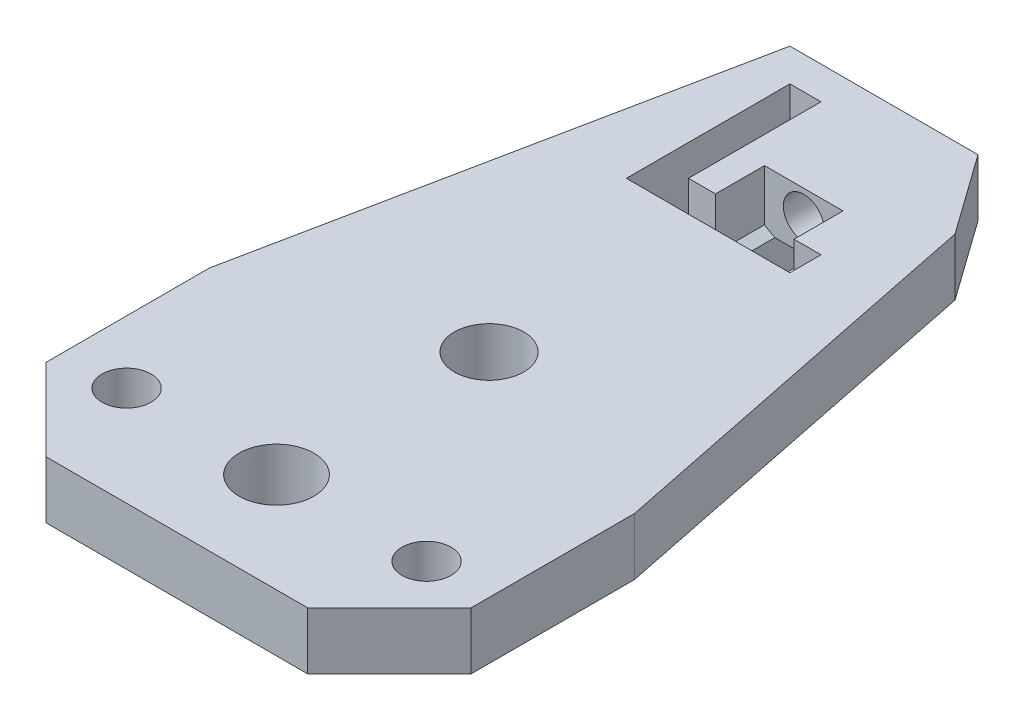
SolidWorks part; units mm, degrees
ref_plane "Front Plane" through (0, 0, 0) normal (0, 0, 1) x (1, 0, 0)
ref_plane "Top Plane" through (0, 0, 0) normal (0, 1, 0) x (1, 0, 0)
ref_plane "Right Plane" through (0, 0, 0) normal (1, 0, 0) x (0, 0, -1)
sketch "Sketch1" plane through (0, 0, 0) normal (0, 1, 0) x (1, 0, 0)
  line L0 (4, 24.01) -> (4, 4)
  line L1 (0, 0) -> (28.01, 0)
  line L2 (0, 0) -> (0, 28.01)
  line L3 (0, 28.01) -> (28.01, 28.01)
  line L4 (28.01, 0) -> (28.01, 28.01)
  line L5 (4, 4) -> (24.01, 4)
  line L6 (24.01, 4) -> (24.01, 7.8)
  line L7 (24.01, 7.8) -> (7.8, 7.8)
  line L8 (7.8, 7.8) -> (7.8, 24.01)
  line L9 (7.8, 24.01) -> (4, 24.01)
  line L10 (24.01, 4) -> (28.01, 4) construction
  line L11 (4, 4) -> (0, 4) construction
  line L12 (4, 4) -> (4, 0) construction
  line L13 (4, 24.01) -> (4, 28.01) construction
  line L14 (28.01, -31) -> (28.01, -61)
  line L15 (0, 0) -> (28.01, 0)
  line L16 (0, 0) -> (0, -61)
  line L17 (0, -61) -> (28.01, -61)
  line L18 (28.01, 0) -> (28.01, -61)
  line L19 (28.01, -61) -> (40.01, -61)
  line L20 (28.01, -61) -> (28.01, -31)
  line L22 (40.01, -61) -> (40.01, -31)
  line L29 (14.005, -61) -> (14.005, 28.01) construction
  line L30 (0, -31) -> (0, -61)
  line L31 (0, -61) -> (-12, -61)
  line L32 (-12, -61) -> (-12, -31)
  line L33 (0, -31) -> (-12, -31)
  line L35 (28.01, -31) -> (28.01, 28.01)
  line L36 (28.01, -61) -> (40.01, -61)
  line L37 (28.01, -61) -> (28.01, -31)
  line L38 (28.01, -31) -> (40.01, -31)
  line L39 (40.01, -61) -> (40.01, -31)
  line L40 (-12, -61) -> (0, -61)
  line L41 (-12, -61) -> (-12, -31)
  line L42 (-12, -31) -> (0, -31)
  line L43 (0, -61) -> (0, -31)
  line L44 (28.01, -31) -> (40.01, -31)
  line L45 (28.01, -31) -> (40.01, -31)
  line L46 (28.01, -31) -> (28.01, 28.01)
  line L49 (-12, -31) -> (0, -31)
  line L52 (0, -31) -> (0, 28.01)
  circle A0 centre (14, -22.8) radius 4.25
  circle A1 centre (14, -48.8) radius 4.575
  circle A2 centre (32.3515, -48.8) radius 3
  circle A3 centre (-4.3415, -48.8) radius 3
  dimension "D9" = 9.15
  dimension "D10" = 6
  dimension "D7" = 8.5
  dimension "D1" = 3.8
  dimension "D2" = 20.01
  dimension "D3" = 4
  dimension "D4" = 65
  dimension "D5" = 10
  dimension "D6" = 26.8
  dimension "D8" = 26
  dimension "D11" = 12
  dimension "D12" = 30
  dimension "D13" = 18.3515
extrude "Boss-Extrude1" add sketch "Sketch1" along normal blind 7 contours L18 L1 L16 L17 A1 A0 | L1 L4 L3 L2 L9 L8 L7 L6 L5 L0 | L41 L40 L43 L42 | L37 L36 L39 L38 | A3 | A2
sketch "Sketch4" plane through (0, 0, 0) normal (0, -1, 0) x (1, 0, 0)
  line L0 (40.01, 31) -> (28.01, -28.01)
  line L1 (28.01, -28.01) -> (28.01, 31)
  line L2 (28.01, 31) -> (40.01, 31)
  line L3 (0, 31) -> (-12, 31)
  line L4 (-12, 31) -> (0, -28.01)
  line L5 (0, -28.01) -> (0, 31)
extrude "Boss-Extrude2" add sketch "Sketch4" against normal up to surface (7 mm away) up to face at (14, 7, 53.375)
sketch "Sketch5" plane through (0, 0, 0) normal (0, -1, 0) x (-1, 0, 0)
  line L0 (-14.005, -61) -> (-14.005, 28.01) construction
  line L1 (-21.505, -44.225) -> (-6.505, -44.225)
  line L2 (-21.505, -44.225) -> (-21.505, -27.05)
  line L3 (-21.505, -27.05) -> (-6.505, -27.05)
  line L4 (-6.505, -44.225) -> (-6.505, -27.05)
  line L5 (12, -61) -> (-40.01, -61) construction
  line L6 (0, 28.01) -> (-28.01, 28.01) construction
  circle A0 centre (-14, -48.8) radius 4.575 construction
  circle A1 centre (-14, -22.8) radius 4.25 construction
  point P14 (-14.005, -27.05)
  dimension "D1" = 15
extrude "Boss-Extrude3" add sketch "Sketch5" along normal blind 15
sketch "Sketch6" plane through (6.505, 0, 0) normal (-1, 0, 0) x (0, 0, 1)
  line L0 (44.225, -8.2) -> (27.05, -8.2) construction
  line L3 (44.225, -15) -> (44.225, 0) construction
  line L4 (27.05, -15) -> (27.05, 0) construction
  line L5 (44.225, 0) -> (27.05, 0) construction
  circle A0 centre (35.6375, -8.2) radius 4.2
  dimension "D1" = 8.4
  dimension "D2" = 8.2
extrude "Cut-Extrude3" cut sketch "Sketch6" against normal through all
sketch "Sketch7" plane through (0, 0, 0) normal (0, -1, 0) x (1, 0, 0)
  line L0 (-2, 61) -> (-12, 51)
  line L1 (-12, 61) -> (40.01, 61) construction
  line L2 (-12, 61) -> (-12, 31) construction
  line L3 (-12, 51) -> (-12, 61)
  line L4 (-12, 61) -> (-2, 61)
  line L5 (40.01, 51) -> (30.01, 61)
  line L6 (40.01, 61) -> (40.01, 31) construction
  line L7 (30.01, 61) -> (40.01, 61)
  line L8 (40.01, 61) -> (40.01, 51)
  line L9 (23.01, -28.01) -> (30.0028, -18.2106)
  line L10 (0, -28.01) -> (28.01, -28.01) construction
  line L11 (28.01, -28.01) -> (40.01, 31) construction
  line L12 (30.0028, -18.2106) -> (28.01, -28.01)
  line L13 (28.01, -28.01) -> (23.01, -28.01)
  dimension "D1" = 5
  dimension "D2" = 10
  dimension "D3" = 10
extrude "Cut-Extrude4" cut sketch "Sketch7" against normal through all
sketch "Sketch8" plane through (0, 0, 0) normal (0, -1, 0) x (-1, 0, 0)
  line L0 (-4, 4) -> (1.3565, -48.5002) construction
  circle A0 centre (4.3415, -48.8) radius 3 construction
  text T0 "     CC" font "Century Gothic" height 8
  dimension "D1" = 52.5002
  dimension "D2" = 13.452
extrude "Cut-Extrude5" cut sketch "Sketch8" against normal blind 2
sketch "Sketch9" plane through (21.505, 0, 0) normal (1, 0, 0) x (0, 0, -1)
  line L0 (-27.05, -15) -> (-32.05, -15)
  line L1 (-27.05, -15) -> (-44.225, -15) construction
  line L2 (-32.05, -15) -> (-27.05, -10)
  line L3 (-27.05, -15) -> (-27.05, 0) construction
  line L4 (-27.05, -10) -> (-27.05, -15)
  line L5 (-44.225, -10) -> (-44.225, -15)
  line L6 (-44.225, -15) -> (-44.225, 0) construction
  line L7 (-44.225, -15) -> (-39.225, -15)
  line L8 (-39.225, -15) -> (-44.225, -10)
  dimension "D1" = 5
extrude "Cut-Extrude6" cut sketch "Sketch9" against normal through all
sketch "Sketch12" plane through (0, 0, 0) normal (0, -1, 0) x (1, 0, 0)
  line L0 (7.8, -24.01) -> (4, -24.01) construction
  line L1 (4, -24.01) -> (4, -4) construction
  line L2 (4, -4) -> (24.01, -4) construction
  line L3 (24.01, -4) -> (24.01, -7.8) construction
  line L4 (24.01, -7.8) -> (7.8, -7.8) construction
  line L5 (7.8, -7.8) -> (7.8, -24.01) construction
  line L6 (7.8, -24.01) -> (4, -24.01)
  line L7 (4, -24.01) -> (4, -4)
  line L8 (4, -4) -> (24.01, -4)
  line L9 (24.01, -4) -> (24.01, -7.8)
  line L10 (24.01, -7.8) -> (7.8, -7.8)
  line L11 (7.8, -7.8) -> (7.8, -24.01)
  line L12 (9.8, -26.01) -> (9.8, -9.8)
  line L13 (9.8, -9.8) -> (26.01, -9.8)
  line L14 (26.01, -9.8) -> (26.01, -2)
  line L15 (26.01, -2) -> (2, -2)
  line L16 (2, -2) -> (2, -26.01)
  line L17 (2, -26.01) -> (9.8, -26.01)
  dimension "D1" = 2
  dimension "D2" = 2
  dimension "D3" = 2
  dimension "D4" = 2
  dimension "D5" = 2
  dimension "D6" = 2
extrude "Boss-Extrude6" add sketch "Sketch12" along normal blind 7
sketch "Sketch2" plane through (0, 0, -7.8) normal (0, 0, 1) x (1, 0, 0)
  line L0 (24.01, 3.5) -> (7.8, 3.5) construction
  line L1 (15.905, 9.0426) -> (11.105, 6.2713)
  line L2 (11.105, 6.2713) -> (11.105, 0.7287)
  line L3 (11.105, 0.7287) -> (15.905, -2.0426)
  line L4 (15.905, -2.0426) -> (20.705, 0.7287)
  line L5 (20.705, 0.7287) -> (20.705, 6.2713)
  line L6 (20.705, 6.2713) -> (15.905, 9.0426)
  line L8 (7.8, 7) -> (7.8, -7) construction
  line L9 (20.705, 6.2713) -> (20.705, 7)
  line L10 (11.105, 0.7287) -> (11.105, 0)
  line L11 (20.705, 7) -> (19.4428, 7)
  line L12 (11.105, 3.5) -> (11.105, 6.2713)
  line L14 (24.01, 0) -> (7.8, 0) construction
  line L15 (11.105, 0) -> (20.705, 0)
  line L16 (20.705, 0) -> (20.705, 0.7287)
  line L17 (7.8, -7) -> (24.01, -7) construction
  line L18 (7.8, -7) -> (24.01, -7)
  line L19 (-2, 3.5) -> (30.01, 3.5) construction
  line L20 (24.01, 7) -> (24.01, -7) construction
  line L21 (24.01, 7) -> (24.01, -7)
  line L22 (7.8, 7) -> (7.8, -7) construction
  line L23 (30.01, 7) -> (-2, 7)
  line L24 (-2, 7) -> (-2, 0)
  line L25 (-2, 0) -> (30.01, 0)
  line L26 (30.01, 0) -> (30.01, 7)
  line L27 (30.01, 7) -> (-2, 7) construction
  line L28 (-2, 7) -> (-2, 0) construction
  line L29 (-2, 0) -> (30.01, 0) construction
  line L30 (30.01, 0) -> (30.01, 7) construction
  line L31 (7.8, 7) -> (7.8, -7)
  line L33 (19.4428, 7) -> (20.705, 6.2713)
  line L34 (11.105, 7) -> (12.3672, 7)
  line L35 (12.3672, 7) -> (11.105, 6.2713)
  line L36 (24.01, 7) -> (7.8, 7) construction
  line L38 (11.105, 6.2713) -> (11.105, 7)
  circle A0 centre (15.905, 3.5) radius 4.8 construction
  point P15 (15.905, 3.5)
  dimension "D1" = 9.6
  dimension "D2" = 0
extrude "Cut-Extrude1" cut sketch "Sketch2" against normal blind 6 contours L1 L2 L3 L4 L5 L6 | L9 L11 L33 | L38 L34 L35
sketch "Sketch3" plane through (0, 0, -13.8) normal (0, 0, 1) x (1, 0, 0)
  line L2 (11.105, 7) -> (11.105, 0.7287) construction
  line L3 (20.705, 0.7287) -> (20.705, 7) construction
  line L5 (11.105, 7) -> (11.105, 0.7287)
  line L6 (20.705, 0.7287) -> (20.705, 7)
  line L7 (20.705, 3.8644) -> (11.105, 3.8644) construction
  circle A0 centre (15.905, 3.8644) radius 2.5
  dimension "D1" = 5
extrude "Cut-Extrude2" cut sketch "Sketch3" against normal through all contours A0 L7 | L7 A0
equation "\"8mm hole\" = 8.4mm'used to be the diameter of the linear motion rods"
equation "\"22mm hole\"= 23mm'this is the size of the hole for the nema 17 standard was 22mm"
equation "\"15mm hole\"= 15.8mm'this is the hole for the linear motion sliders, they are all set to this measurement so if you have different sized bearing sliders you may have to adjust individually"
equation "\"bed height offset\"= 3mm'this is how far the bed has been offset from a low point (probably don't want to edit, but can)"
equation "\"motor width\"= 42.5mm"
equation "\"D9@Sketch1\"=\"8mm hole\" + .75"
equation "\"D7@Sketch1\"= \"lin_rd_diam\" + \"lin_rd_vert_hole_tol\""
equation "\"#10 nut width\"= 9.6mm'this is the width of a nut from flat side to other flat side"
equation "\"#10 bolt diameter\"= 5mm'This is the diameter including the threads"
equation "\"Al_width\"= 19.31mm'Self explainatory"
equation "\"Al_thick\"= 3.35mm"
equation "\"lin_rd_vert_hole_tol\"= 0.5mm"
equation "\"lin_rd_horz_hole_tol\"= 0.5mm"
equation "\"lin_rd_diam\"= 8mm"
equation "\"slid_diam\"= 15mm"
equation "\"slid_vert_tol\"= 0.7mm"
equation "\"mot_face_ridge_diam\"= 22mm"
equation "\"mot_face_ridge_tol\"= 1mm"
equation "\"slid_horz_tol\"= 0.8"
equation "\"Al_thick_tol\" = 0.45mm"
equation "\"Al_width_tol\" = 0.7mm"
equation "\"D2@Sketch1\"= \"Al_width\" + \"Al_width_tol\""
equation "\"D1@Sketch1\"= \"Al_thick\" + \"Al_thick_tol\""
equation "\"D1@Sketch2\"= \"#10 nut width\""
